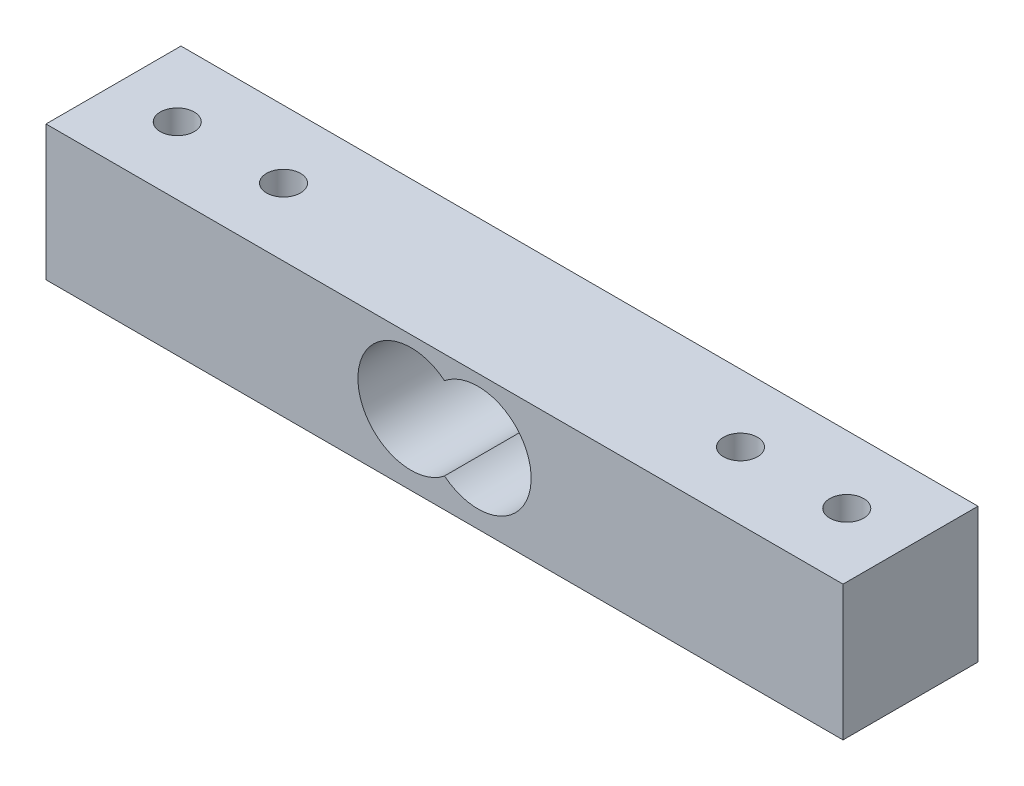
SolidWorks part; units mm, degrees
ref_plane "Front Plane" through (0, 0, 0) normal (0, 0, 1) x (1, 0, 0)
ref_plane "Top Plane" through (0, 0, 0) normal (0, 1, 0) x (1, 0, 0)
ref_plane "Right Plane" through (0, 0, 0) normal (1, 0, 0) x (0, 0, -1)
sketch "Sketch2" plane through (0, 0, 0) normal (0, 1, 0) x (1, 0, 0)
  line L2 (-26.2255, 6.5723) -> (48.7745, 6.5723)
  line L3 (-26.2255, 6.5723) -> (-26.2255, -6.1277)
  line L4 (-26.2255, -6.1277) -> (48.7745, -6.1277)
  line L5 (48.7745, 6.5723) -> (48.7745, -6.1277)
  dimension "D1" = 12.7
  dimension "80" = 75
extrude "Boss-Extrude1" add sketch "Sketch2" along normal blind 12.7
sketch "Sketch3" plane through (0, 0, 6.1277) normal (0, 0, 1) x (1, 0, 0)
  line L0 (11.2745, 24.5435) -> (11.2745, -10.2244) construction
  line L1 (-26.2255, 12.7) -> (-26.2255, 0) construction
  circle A0 centre (8.1245, 6.6483) radius 5
  arc A1 (11.2745, 2.7653) -> (11.2745, 10.5312) centre (14.4245, 6.6483) ccw
  dimension "D2" = 10
  dimension "D3" = 10
  dimension "D1" = 37.5
  dimension "D4" = 6.3
  dimension "D5" = 3.15
extrude "Cut-Extrude1" cut sketch "Sketch3" against normal blind 12.7 contours L0 A0 | A0 L0 | A0 A1
sketch "Sketch4" plane through (0, 12.7, 0) normal (0, 1, 0) x (1, 0, 0)
  line L0 (11.2745, 18.927) -> (11.2745, -15.0739) construction
  line L1 (-26.2255, 6.5723) -> (-26.2255, -6.1277) construction
  line L2 (-26.2255, -6.1277) -> (48.7745, -6.1277) construction
  circle A0 centre (-20.2255, 0.2223) radius 1.6
  circle A1 centre (-10.2255, 0.2222) radius 1.6
  circle A2 centre (32.7745, 0.2222) radius 1.6
  circle A3 centre (42.7745, 0.2222) radius 1.6
  dimension "D7" = 3.2
  dimension "D8" = 3.2
  dimension "D1" = 10
  dimension "D2" = 10
  dimension "D3" = 43
  dimension "D4" = 37.5
  dimension "D5" = 21.5
  dimension "D6" = 6.35
extrude "Cut-Extrude2" cut sketch "Sketch4" against normal through all
